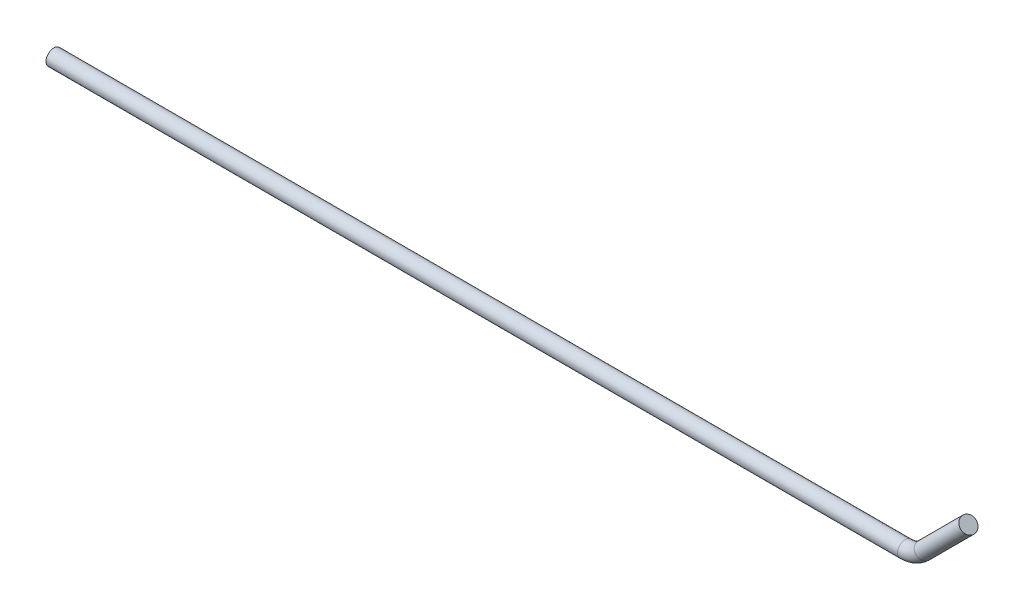
SolidWorks part; units mm, degrees
ref_plane "Спереди" through (0, 0, 0) normal (0, 0, 1) x (1, 0, 0)
ref_plane "Сверху" through (0, 0, 0) normal (0, 1, 0) x (1, 0, 0)
ref_plane "Справа" through (0, 0, 0) normal (1, 0, 0) x (0, 0, -1)
sketch "Эскиз17" plane through (0, 0, 0) normal (0, 0, 1) x (1, 0, 0)
  line L0 (0, 0) -> (325.8579, 0)
  line L1 (332.9289, 2.9289) -> (350, 20)
  arc A0 (325.8579, 0) -> (332.9289, 2.9289) centre (325.8579, 10) ccw
  point P6 (330, 0)
  dimension "D4" = 10
  dimension "D1" = 330
  dimension "D2" = 20
  dimension "D3" = 135
sweep "По траектории1" add path "Эскиз17" circular profile diameter 6 parameters "D3"=6
